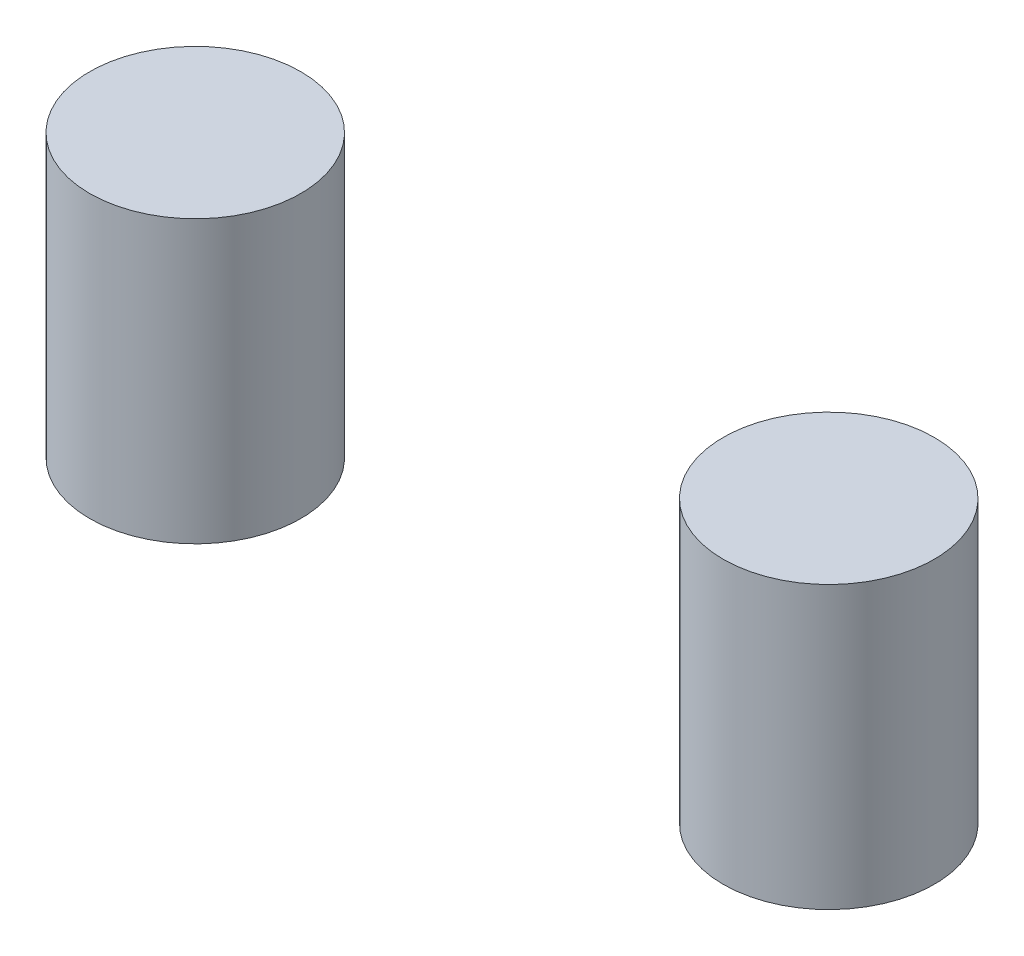
SolidWorks part; units mm, degrees
ref_plane "前视基准面" through (0, 0, 0) normal (0, 0, 1) x (1, 0, 0)
ref_plane "上视基准面" through (0, 0, 0) normal (0, 1, 0) x (1, 0, 0)
ref_plane "右视基准面" through (0, 0, 0) normal (1, 0, 0) x (0, 0, -1)
sketch "草图1" plane through (0, 0, 0) normal (0, 1, 0) x (1, 0, 0)
  line L0 (-90, 0) -> (90, 0) construction
  circle A0 centre (-90, 0) radius 30
  circle A1 centre (90, 0) radius 30
  point P4 (0, 0)
  dimension "D2" = 60
  dimension "D1" = 180
extrude "凸台-拉伸1" add sketch "草图1" along normal blind 80
